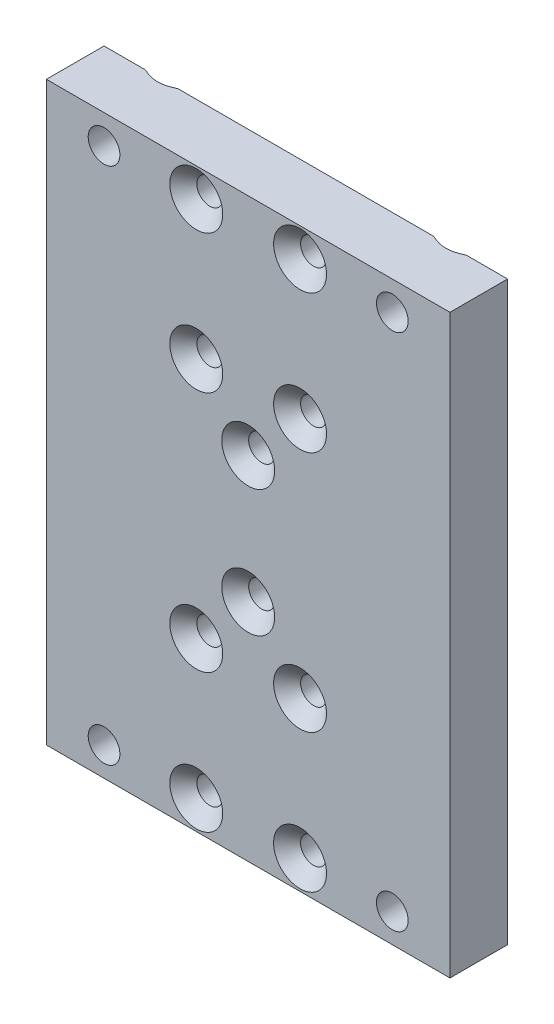
SolidWorks part; units mm, degrees
ref_plane "Front Plane" through (0, 0, 0) normal (0, 0, 1) x (1, 0, 0)
ref_plane "Top Plane" through (0, 0, 0) normal (0, 1, 0) x (1, 0, 0)
ref_plane "Right Plane" through (0, 0, 0) normal (1, 0, 0) x (0, 0, -1)
sketch "Sketch1" plane through (0, 0, 0) normal (0, 0, 1) x (1, 0, 0)
  line L1 (35, -50) -> (-35, -50)
  line L2 (35, -50) -> (35, 50)
  line L3 (35, 50) -> (-35, 50)
  line L4 (-35, -50) -> (-35, 50)
  line L5 (35, -50) -> (-35, 50) construction
  line L6 (35, 50) -> (-35, -50) construction
  point P0 (0, 0)
  dimension "D1" = 70
  dimension "D2" = 100
extrude "Boss-Extrude1" add sketch "Sketch1" along normal blind 10
sketch "Sketch2" plane through (0, 0, 0) normal (0, 0, -1) x (-1, 0, 0)
  line L0 (0, 50) -> (0, 0) construction
  line L1 (-35, 50) -> (35, 50) construction
  line L2 (0, 0) -> (-35, 0) construction
  line L3 (-35, -50) -> (-35, 50) construction
  circle A0 centre (-25, 45) radius 2.5
  circle A1 centre (25, 45) radius 2.5
  circle A2 centre (-25, -45) radius 2.5
  circle A3 centre (25, -45) radius 2.5
  dimension "D1" = 5
  dimension "D2" = 5
  dimension "D3" = 10
extrude "Cut-Extrude1" cut sketch "Sketch2" against normal through all
sketch "Sketch3" plane through (0, 0, 0) normal (0, 0, -1) x (-1, 0, 0)
  circle A1 centre (9, 21) radius 1.5
  circle A2 centre (9, 21) radius 1.5
  circle A3 centre (9, 45) radius 1.5
  circle A4 centre (9, 45) radius 1.5
  circle A5 centre (-9, 21) radius 1.5
  circle A6 centre (-9, 21) radius 1.5
  circle A7 centre (-9, 45) radius 1.5
  circle A8 centre (-9, 45) radius 1.5
  circle A9 centre (9, -45) radius 1.5
  circle A10 centre (9, -45) radius 1.5
  circle A11 centre (9, -21) radius 1.5
  circle A12 centre (9, -21) radius 1.5
  circle A13 centre (-9, -45) radius 1.5
  circle A14 centre (-9, -45) radius 1.5
  circle A15 centre (-9, -21) radius 1.5
  circle A16 centre (-9, -21) radius 1.5
  dimension "D1" = 0
  dimension "D2" = 0
  dimension "D3" = 0
  dimension "D4" = 0
  dimension "D5" = 0
  dimension "D6" = 0
  dimension "D7" = 0
  dimension "D8" = 0
extrude "Cut-Extrude2" cut sketch "Sketch3" against normal through all
sketch "Sketch4" plane through (0, 0, 10) normal (0, 0, 1) x (1, 0, 0)
  line L0 (0, 50) -> (0, 0) construction
  line L1 (35, 50) -> (-35, 50) construction
  line L2 (0, 0) -> (-35, 0) construction
  line L3 (-35, 50) -> (-35, -50) construction
  line L4 (0, 33) -> (-35, 33) construction
  circle A0 centre (-9, 45) radius 3.45
  circle A1 centre (-9, 21) radius 3.45
  circle A2 centre (9, 21) radius 3.45
  circle A3 centre (9, 45) radius 3.45
  circle A4 centre (9, -21) radius 3.45
  circle A5 centre (-9, -21) radius 3.45
  circle A6 centre (-9, -45) radius 3.45
  circle A7 centre (9, -45) radius 3.45
  dimension "D1" = 6.9
extrude "Cut-Extrude3" [suppressed] cut sketch "Sketch4" against normal blind 4
sketch "Sketch5" plane through (0, 0, 10) normal (0, 0, 1) x (1, 0, 0)
  circle A1 centre (0, -11) radius 2
  circle A2 centre (0, -11) radius 2
  circle A3 centre (0, 11) radius 2
  circle A4 centre (0, 11) radius 2
  dimension "D1" = 0
  dimension "D2" = 0
extrude "Cut-Extrude4" cut sketch "Sketch5" against normal through all
sketch "Sketch6" plane through (0, 0, 10) normal (0, 0, 1) x (1, 0, 0)
  circle A0 centre (0, 11) radius 3.5
  circle A1 centre (0, -11) radius 3.5
  dimension "D1" = 7
extrude "Cut-Extrude5" [suppressed] cut sketch "Sketch6" against normal blind 4
hole_wizard "CSK for M4 socket countersunk head screw1" positions "Sketch9" profile "Sketch10" countersink size "M4" standard "DIN" end condition through all
sketch "Sketch9" plane through (0, 0, 10) normal (0, 0, 1) x (1, 0, 0)
  point P0 (-9, 45)
  point P3 (9, 45)
  point P6 (9, 21)
  point P9 (-9, 21)
  point P12 (0, 11)
  point P15 (0, -11)
  point P18 (9, -21)
  point P21 (-9, -21)
  point P24 (-9, -45)
  point P27 (9, -45)
sketch "Sketch10" plane through (-9, 45, 10) normal (1, 0, 0) x (0, -1, 0)
  line L0 (0, 0) -> (0, 10)
  line L1 (0, 10) -> (2.25, 10)
  line L2 (2.25, 10) -> (2.25, 2.34)
  line L3 (2.25, 2.34) -> (4.59, 0)
  line L5 (4.59, 0) -> (0, 0)
  line L6 (-2.25, 2.34) -> (-4.59, 0) construction
  line L11 (0, -6.35) -> (0, 107.95) construction
  dimension "Thru Hole Dia." = 4.5
  dimension "Thru Hole Depth" = 10
  dimension "Near C'Sink Dia." = 9.18
  dimension "Near C'Sink Angle" = 90
hole_wizard "CSK for M5 socket countersunk head screw2" positions "Sketch11" profile "Sketch12" countersink size "M5" standard "DIN" end condition through all
sketch "Sketch11" plane through (0, 0, 0) normal (0, 0, -1) x (-1, 0, 0)
  point P0 (-25, 45)
  point P3 (25, 45)
  point P6 (25, -45)
  point P9 (-25, -45)
sketch "Sketch12" plane through (25, 45, 0) normal (1, 0, 0) x (0, 1, 0)
  line L0 (0, 0) -> (0, 10)
  line L1 (0, 10) -> (2.75, 10)
  line L2 (2.75, 10) -> (2.75, 2.985)
  line L3 (2.75, 2.985) -> (5.735, 0)
  line L5 (5.735, 0) -> (0, 0)
  line L6 (-2.75, 2.985) -> (-5.735, 0) construction
  line L11 (0, -6.35) -> (0, 107.95) construction
  dimension "Thru Hole Dia." = 5.5
  dimension "Thru Hole Depth" = 10
  dimension "Near C'Sink Dia." = 11.47
  dimension "Near C'Sink Angle" = 90
